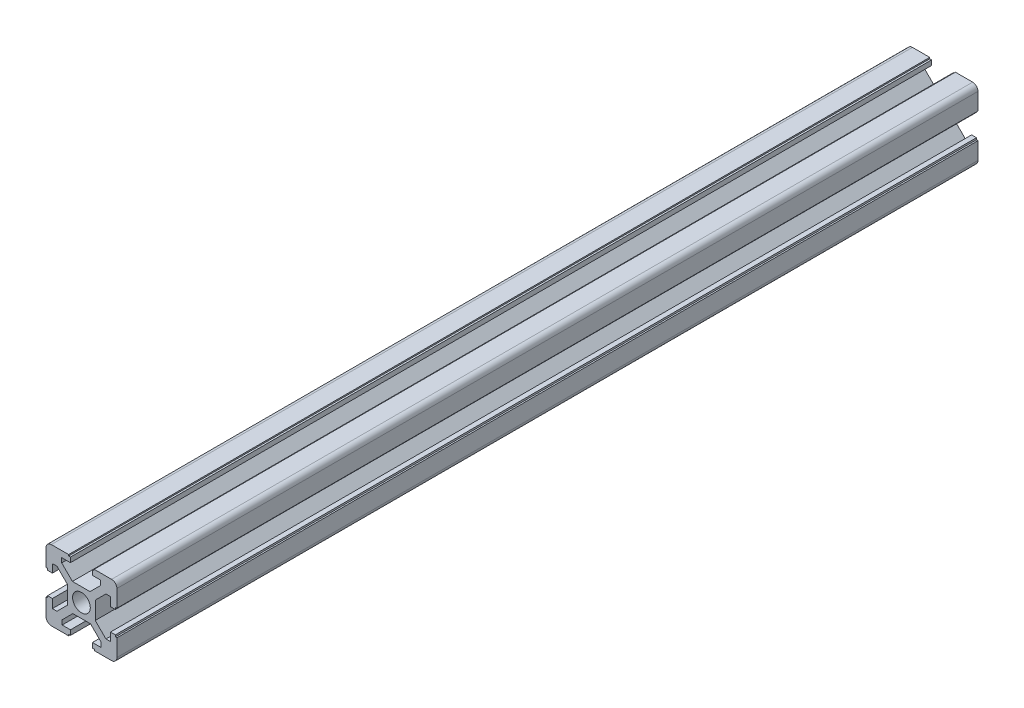
SolidWorks part; units mm, degrees
ref_plane "Front Plane" through (0, 0, 0) normal (0, 0, 1) x (1, 0, 0)
ref_plane "Top Plane" through (0, 0, 0) normal (0, 1, 0) x (1, 0, 0)
ref_plane "Right Plane" through (0, 0, 0) normal (1, 0, 0) x (0, 0, -1)
sketch "Sketch1" plane through (0, 0, 0) normal (0, 0, 1) x (1, 0, 0)
  line L0 (240.9169, 601.7923) -> (1204.5843, 601.7923) construction
  line L6 (13.0291, 10.3872) -> (13.0291, 12.8554)
  line L7 (12.7291, 6.0212) -> (29.7291, 6.0212)
  line L11 (11.2291, 7.5212) -> (11.2291, 24.3895)
  line L12 (12.7291, 25.8895) -> (29.7291, 25.8895)
  line L13 (31.2291, 7.5212) -> (31.2291, 24.3895)
  line L14 (11.2291, 6.0212) -> (31.2291, 25.8895) construction
  line L15 (11.2291, 25.8895) -> (31.2291, 6.0212) construction
  line L16 (13.0291, 24.0895) -> (13.041, 24.0895)
  line L17 (29.4291, 10.5205) -> (29.4291, 12.8554)
  line L18 (13.0291, 7.8212) -> (13.041, 7.8212)
  line L19 (11.2291, 15.9554) -> (31.2291, 15.9554) construction
  line L20 (11.6567, 12.8554) -> (13.0291, 12.8554)
  line L21 (11.6567, 19.0554) -> (13.0291, 19.0554)
  line L22 (21.2291, 6.0212) -> (21.2291, 25.8895) construction
  line L23 (24.8338, 25.9554) -> (24.8338, 25.5277)
  line L24 (17.3291, 21.0535) -> (17.3291, 19.8297)
  line L25 (11.2291, 19.56) -> (11.6567, 19.56)
  line L26 (11.6567, 19.56) -> (11.6567, 19.0554)
  line L27 (11.6567, 19.0554) -> (13.0291, 19.0554)
  line L28 (17.3291, 18.3778) -> (14.3166, 21.3903)
  line L29 (14.3166, 21.3903) -> (13.0291, 21.3903)
  line L30 (17.3291, 13.3997) -> (14.3166, 10.3872)
  line L31 (14.3166, 10.3872) -> (13.0291, 10.3872)
  line L32 (13.0291, 7.8212) -> (13.0291, 24.0895) construction
  line L33 (29.4172, 7.8212) -> (29.4291, 7.8212)
  line L34 (13.0291, 7.8212) -> (29.4291, 7.8212) construction
  line L35 (17.3291, 12.081) -> (17.3291, 10.641)
  line L36 (24.8338, 25.5277) -> (24.3291, 25.5277)
  line L37 (11.2291, 12.8554) -> (31.2291, 12.8554) construction
  line L38 (24.3291, 25.5277) -> (24.3291, 24.1554)
  line L39 (11.2291, 19.0554) -> (31.2291, 19.0554) construction
  line L40 (17.3291, 18.3778) -> (17.3291, 13.3997)
  line L41 (11.6567, 12.8554) -> (11.6567, 12.3367)
  line L42 (11.6567, 12.3367) -> (11.2291, 12.3367)
  line L43 (13.0291, 19.0554) -> (13.0291, 21.3903)
  line L44 (24.3291, 24.1554) -> (26.664, 24.1554)
  line L45 (26.664, 22.8679) -> (26.664, 24.1554)
  line L46 (23.6515, 19.8554) -> (26.664, 22.8679)
  line L47 (23.6515, 19.8554) -> (18.6734, 19.8554)
  line L48 (18.6734, 19.8554) -> (15.661, 22.8679)
  line L49 (15.661, 24.1554) -> (18.1291, 24.1554)
  line L50 (15.661, 22.8679) -> (15.661, 24.1554)
  line L51 (18.1291, 25.5277) -> (18.1291, 24.1554)
  line L52 (18.1291, 25.5277) -> (17.6104, 25.5277)
  line L53 (17.6104, 25.5277) -> (17.6104, 25.9554)
  line L54 (31.2291, 12.3507) -> (30.8015, 12.3507)
  line L55 (30.8015, 12.3507) -> (30.8015, 12.8554)
  line L56 (30.8015, 12.8554) -> (29.4291, 12.8554)
  line L57 (29.4291, 12.8554) -> (29.4291, 10.5205)
  line L58 (28.1416, 10.5205) -> (29.4291, 10.5205)
  line L59 (25.1291, 13.533) -> (28.1416, 10.5205)
  line L60 (25.1291, 13.533) -> (25.1291, 18.511)
  line L61 (25.1291, 18.511) -> (28.1416, 21.5235)
  line L62 (29.4291, 21.5235) -> (29.4291, 19.0554)
  line L63 (28.1416, 21.5235) -> (29.4291, 21.5235)
  line L64 (30.8015, 19.0554) -> (29.4291, 19.0554)
  line L65 (30.8015, 19.0554) -> (30.8015, 19.5741)
  line L66 (30.8015, 19.5741) -> (31.2291, 19.5741)
  line L67 (17.6244, 5.9554) -> (17.6244, 6.383)
  line L68 (17.6244, 6.383) -> (18.1291, 6.383)
  line L69 (18.1291, 6.383) -> (18.1291, 7.7554)
  line L70 (18.1291, 7.7554) -> (15.7942, 7.7554)
  line L71 (15.7942, 9.0429) -> (15.7942, 7.7554)
  line L72 (18.8067, 12.0554) -> (15.7942, 9.0429)
  line L73 (18.8067, 12.0554) -> (23.7848, 12.0554)
  line L74 (23.7848, 12.0554) -> (26.7973, 9.0429)
  line L75 (26.7973, 7.7554) -> (24.3291, 7.7554)
  line L76 (26.7973, 9.0429) -> (26.7973, 7.7554)
  line L77 (24.3291, 6.383) -> (24.3291, 7.7554)
  line L78 (24.3291, 6.383) -> (24.8478, 6.383)
  line L79 (24.8478, 6.383) -> (24.8478, 5.9554)
  line L80 (29.4172, 24.0895) -> (29.4291, 24.0895)
  line L81 (13.0291, 24.0895) -> (29.4291, 24.0895) construction
  line L82 (29.4291, 19.0554) -> (29.4291, 21.5235)
  line L83 (29.4291, 7.8212) -> (29.4291, 24.0895) construction
  circle A1 centre (21.2291, 15.9554) radius 2.5
  arc A2 (12.7291, 25.8895) -> (11.2291, 24.3895) centre (12.7291, 24.3895) ccw
  arc A3 (11.2291, 7.5212) -> (12.7291, 6.0212) centre (12.7291, 7.5212) ccw
  arc A4 (29.7291, 6.0212) -> (31.2291, 7.5212) centre (29.7291, 7.5212) ccw
  arc A5 (31.2291, 24.3895) -> (29.7291, 25.8895) centre (29.7291, 24.3895) ccw
  arc A6 (13.0291, 24.0895) -> (13.0291, 24.0895) centre (13.0291, 24.0895) ccw
  arc A7 (29.4291, 24.0895) -> (29.4291, 24.0895) centre (29.4291, 24.0895) ccw
  arc A8 (29.4291, 7.8212) -> (29.4291, 7.8212) centre (29.4291, 7.8212) ccw
  arc A9 (13.0291, 7.8212) -> (13.0291, 7.8212) centre (13.0291, 7.8212) ccw
  point P105 (21.2291, 15.9554)
  dimension "D1" = 20
  dimension "D2" = 1.5
  dimension "D3" = 1.5
  dimension "D7" = 4
  dimension "D8" = 6.1
  dimension "D4" = 1.8
  dimension "D5" = 3.1
  dimension "D6" = 3.1
extrude "Boss-Extrude1" add sketch "Sketch1" along normal blind 243
